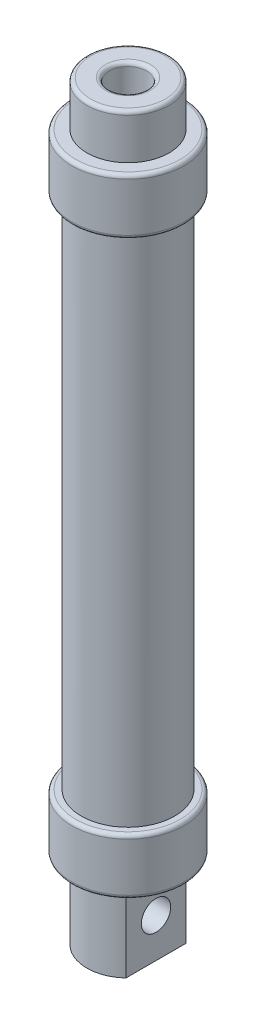
SolidWorks part; units mm, degrees
ref_plane "Front Plane" through (0, 0, 0) normal (0, 0, 1) x (1, 0, 0)
ref_plane "Top Plane" through (0, 0, 0) normal (0, 1, 0) x (1, 0, 0)
ref_plane "Right Plane" through (0, 0, 0) normal (1, 0, 0) x (0, 0, -1)
sketch "Sketch5" plane through (0, 0, 0) normal (0, 1, 0) x (1, 0, 0)
  circle A0 centre (0, 0) radius 12.5
  circle A1 centre (0, 0) radius 10.5
  dimension "D1" = 25
  dimension "D2" = 2
extrude "Boss-Extrude2" add sketch "Sketch5" along normal blind 140
sketch "Sketch6" plane through (0, 140, 0) normal (0, 1, 0) x (1, 0, 0)
  circle A0 centre (0, 0) radius 15
  circle A1 centre (0, 0) radius 11.5438
  dimension "D1" = 30
extrude "Boss-Extrude3" add sketch "Sketch6" along normal blind 14 and the other way blind 1
sketch "Sketch7" plane through (0, 0, 0) normal (0, -1, 0) x (1, 0, 0)
  circle A0 centre (0, 0) radius 15
  circle A1 centre (0, 0) radius 11.5528
  dimension "D1" = 30
extrude "Boss-Extrude4" add sketch "Sketch7" along normal blind 14 and the other way blind 1
fillet "Fillet1" radius 1 1 edges at (0, 139, 15)
fillet "Fillet2" radius 1 1 edges at (0, 1, -15)
fillet "Fillet3" radius 1 1 edges at (0, 154, 15)
fillet "Fillet4" radius 1 1 edges at (0, -14, -15)
sketch "Sketch8" plane through (0, 154, 0) normal (0, 1, 0) x (1, 0, 0)
  circle A0 centre (0, 0) radius 12.5932
extrude "Boss-Extrude5" add sketch "Sketch8" against normal blind 1
sketch "Sketch9" plane through (0, -14, 0) normal (0, -1, 0) x (1, 0, 0)
  circle A0 centre (0, 0) radius 12.7373
extrude "Boss-Extrude6" add sketch "Sketch9" against normal blind 1
sketch "Sketch10" plane through (0, -14, 0) normal (0, -1, 0) x (1, 0, 0)
  circle A0 centre (0, 0) radius 11
  dimension "D1" = 22
extrude "Boss-Extrude7" add sketch "Sketch10" along normal blind 21
sketch "Sketch11" plane through (0, -35, 0) normal (0, -1, 0) x (1, 0, 0)
  line L0 (-11, 0) -> (-7.5, 0) construction
  line L1 (-7.5, 8.0467) -> (-7.5, 0)
  line L2 (-7.5, 0) -> (-7.5, -8.0467)
  line L4 (7.5, 0) -> (7.5, -8.0467)
  line L5 (7.5, 8.0467) -> (7.5, 0)
  line L6 (7.5, 0) -> (11, 0) construction
  arc A0 (-7.5, 8.0467) -> (-7.5, -8.0467) centre (0, 0) ccw
  arc A1 (7.5, -8.0467) -> (7.5, 8.0467) centre (0, 0) ccw
  dimension "D2" = 22
  dimension "D1" = 7.5
  dimension "D3" = 8.0467
  dimension "D4" = 8.0467
extrude "Cut-Extrude1" cut sketch "Sketch11" against normal blind 21
sketch "Sketch12" plane through (-7.5, 0, 0) normal (-1, 0, 0) x (0, 0, 1)
  line L0 (8.0467, -14) -> (-8.0467, -35) construction
  line L1 (8.0467, -35) -> (-8.0467, -14) construction
  circle A0 centre (0, -24.5) radius 3.935
  dimension "D1" = 7.87
extrude "Cut-Extrude2" cut sketch "Sketch12" against normal through all
sketch "Sketch13" plane through (0, 154, 0) normal (0, 1, 0) x (1, 0, 0)
  circle A0 centre (0, 0) radius 11
  dimension "D1" = 22
extrude "Boss-Extrude8" add sketch "Sketch13" along normal blind 12
sketch "Sketch14" plane through (0, 166, 0) normal (0, 1, 0) x (1, 0, 0)
  circle A0 centre (0, 0) radius 5
  dimension "D1" = 10
extrude "Cut-Extrude3" cut sketch "Sketch14" against normal blind 20
fillet "Fillet5" radius 1 1 edges at (0, 166, 11)
fillet "Fillet6" radius 1 1 edges at (0, 166, 5)
